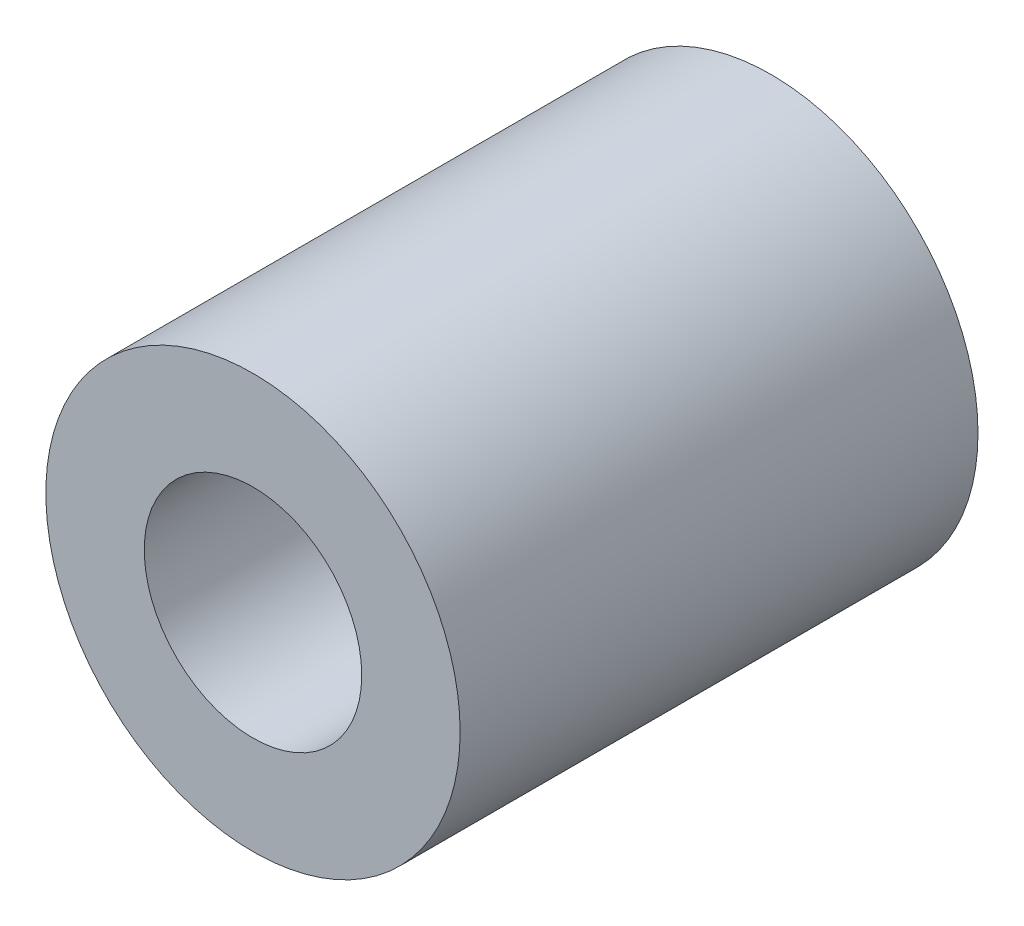
SolidWorks part; units mm, degrees
ref_plane "前视基准面" through (0, 0, 0) normal (0, 0, 1) x (1, 0, 0)
ref_plane "上视基准面" through (0, 0, 0) normal (0, 1, 0) x (1, 0, 0)
ref_plane "右视基准面" through (0, 0, 0) normal (1, 0, 0) x (0, 0, -1)
sketch "草图1" plane through (0, 0, 0) normal (0, 0, 1) x (1, 0, 0)
  circle A0 centre (0, 0) radius 4
  circle A1 centre (0, 0) radius 2.1
  dimension "D1" = 8
  dimension "D2" = 4.2
extrude "凸台-拉伸1" add sketch "草图1" along normal mid plane 10
